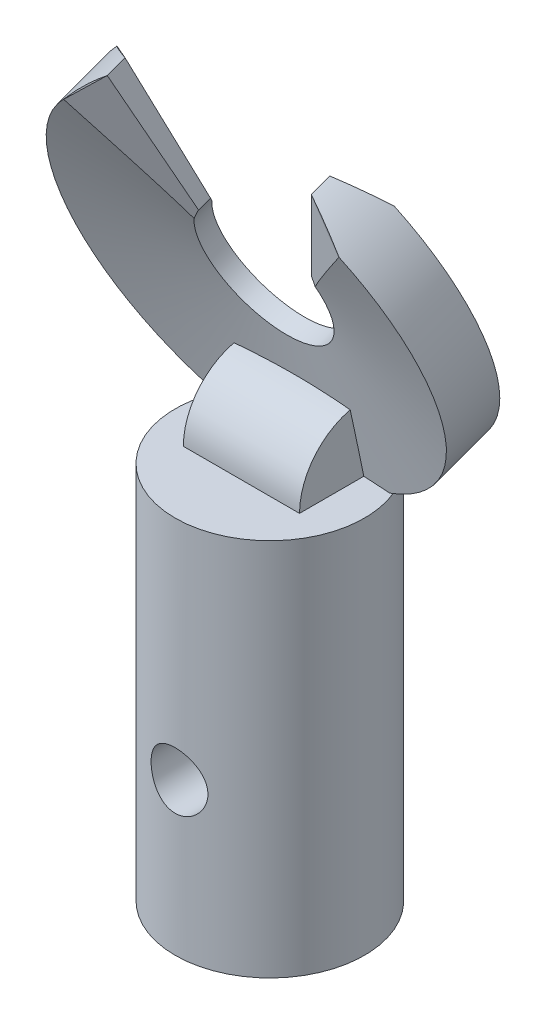
SolidWorks part; units mm, degrees
ref_plane "Front Plane" through (0, 0, 0) normal (0, 0, 1) x (1, 0, 0)
ref_plane "Top Plane" through (0, 0, 0) normal (0, 1, 0) x (1, 0, 0)
ref_plane "Right Plane" through (0, 0, 0) normal (1, 0, 0) x (0, 0, -1)
sketch "Sketch1" plane through (0, 0, 0) normal (0, 1, 0) x (1, 0, 0)
  line L1 (-15, 15) -> (15, 15)
  line L2 (-15, 15) -> (-15, -15)
  line L3 (-15, -15) -> (15, -15)
  line L4 (15, 15) -> (15, -15)
  line L5 (-15, 15) -> (15, -15) construction
  line L6 (-15, -15) -> (15, 15) construction
  point P0 (0, 0)
  dimension "D1" = 30
  dimension "D2" = 30
extrude "Boss-Extrude1" add sketch "Sketch1" along normal blind 3
sketch "Sketch2" plane through (0, 3, 0) normal (0, 1, 0) x (1, 0, 0)
  circle A0 centre (0, -2) radius 5
extrude "Boss-Extrude2" add sketch "Sketch2" along normal blind 55
sketch "Sketch3" plane through (0, 58, 0) normal (0, 1, 0) x (1, 0, 0)
  line L0 (-4.505, 3) -> (6.0136, 3)
  line L1 (15, 15) -> (-15, 15) construction
  circle A1 centre (0, -2) radius 5 construction
ref_plane "Plane1" through (0, 7.7489, -21.2899) normal (0, 0.342, -0.9397) x (1, 0, 0)
sketch "Sketch4" plane through (0, 0, 0) normal (1, 0, 0) x (0, 0, -1)
  line L0 (2.9957, 58.0118) -> (0.1766, 56.9858)
  line L1 (27.1793, -8.432) -> (15.4005, 23.9298) construction
  line L2 (0.1766, 56.9858) -> (-1.1068, 63.4358)
  line L4 (-1.1068, 63.4358) -> (-0.1671, 63.7778)
  line L6 (-0.1671, 63.7778) -> (2.9957, 58.0118)
  line L7 (1.5862, 57.4988) -> (-3.4595, 71.3617) construction
  line L8 (2.1162, 68.3335) -> (-6.6807, 65.1317) construction
  dimension "D1" = 3
  dimension "D2" = 1
  dimension "D3" = 0.5
  dimension "D4" = 6.5
  dimension "D5" = 10
revolve "Revolve1" add sketch "Sketch4" angle 360 about L8
sketch "Sketch5" plane through (0, 7.7489, -21.2899) normal (0, 0.342, -0.9397) x (1, 0, 0)
  line L0 (0, -64.2507) -> (0, -78.6334) construction
  line L1 (-3, -65.2915) -> (-6.5722, -75.1059)
  line L2 (3, -65.2915) -> (6.5722, -75.1059)
  line L3 (-3, -65.2915) -> (3, -65.2915)
  line L4 (-6.5722, -75.1059) -> (6.5722, -75.1059)
  circle A0 centre (0, -63.4887) radius 3.5 construction
  dimension "D1" = 20
  dimension "D2" = 3
extrude "Cut-Extrude2" cut sketch "Sketch5" against normal blind 55
ref_plane "Plane2" through (37.6382, 42.1503, 15.3415) normal (0.6428, 0.7198, 0.262) x (0, -0.342, 0.9397)
sketch "Sketch6" plane through (37.6382, 42.1503, 15.3415) normal (0.6428, 0.7198, 0.262) x (0, -0.342, 0.9397)
  line L0 (-22.6562, -42.0763) -> (-22.6562, -39.5763)
  line L1 (-22.6562, -39.5763) -> (-21.6562, -42.0763)
  line L2 (-22.6562, -42.0763) -> (-19.6562, -42.0763) construction
  line L3 (-21.6562, -42.0763) -> (-22.6562, -42.0763)
  line L4 (-21.1363, -42.0763) -> (-21.1363, -38.1037) construction
  line L5 (-19.6163, -42.0763) -> (-19.6163, -39.5763)
  line L6 (-20.6163, -42.0763) -> (-19.6163, -42.0763)
  line L7 (-19.6163, -39.5763) -> (-20.6163, -42.0763)
  dimension "D1" = 1
  dimension "D2" = 2.5
extrude "Cut-Extrude3" cut sketch "Sketch6" against normal blind 7 draft 9 and the other way blind 2 draft outward yes
ref_plane "Plane3" through (-37.6382, 42.1503, 15.3415) normal (0.6428, -0.7198, -0.262) x (0, 0.342, -0.9397)
sketch "Sketch8" plane through (-37.6382, 42.1503, 15.3415) normal (0.6428, -0.7198, -0.262) x (0, 0.342, -0.9397)
  line L0 (22.6562, 42.0763) -> (22.6562, 39.5763)
  line L1 (22.6562, 39.5763) -> (21.6562, 42.0763)
  line L2 (19.6562, 42.0763) -> (22.6562, 42.0763) construction
  line L3 (21.6562, 42.0763) -> (22.6562, 42.0763)
  line L4 (21.1562, 42.0763) -> (21.1562, 37.0421) construction
  line L5 (20.6562, 42.0763) -> (19.6562, 42.0763)
  line L6 (19.6562, 42.0763) -> (19.6562, 39.5763)
  line L7 (19.6562, 39.5763) -> (20.6562, 42.0763)
  dimension "D1" = 1
  dimension "D2" = 2.5
extrude "Cut-Extrude4" cut sketch "Sketch8" along normal blind 7 draft 9 and the other way blind 2 draft 9
sketch "Sketch10" plane through (0, 58, 0) normal (0, 1, 0) x (1, 0, 0)
  line L0 (-4.5826, 0) -> (4.5826, 0)
  arc A1 (-4.5826, 0) -> (4.5826, 0) centre (0, -2) ccw
  circle A2 centre (0, -2) radius 5 construction
  dimension "D2" = 10
revolve "Revolve2" [suppressed] add sketch "Sketch10" angle 90 about L0
sketch "Sketch11" plane through (0, 0, 0) normal (1, 0, 0) x (0, 0, -1)
  line L1 (-18.3794, -2.1859) -> (24.0775, -2.1859)
  line L2 (-18.3794, -2.1859) -> (-18.3794, 37.7012)
  line L3 (-18.3794, 37.7012) -> (24.0775, 37.7012)
  line L4 (24.0775, -2.1859) -> (24.0775, 37.7012)
extrude "Cut-Extrude5" cut sketch "Sketch11" against normal through all and the other way through all
sketch "Sketch12" plane through (0, 37.7012, 0) normal (0, -1, 0) x (1, 0, 0)
  line L1 (-15, 15) -> (15, 15)
  line L2 (-15, 15) -> (-15, -15)
  line L3 (-15, -15) -> (15, -15)
  line L4 (15, 15) -> (15, -15)
  line L5 (-15, 15) -> (15, -15) construction
  line L6 (-15, -15) -> (15, 15) construction
  point P0 (0, 0)
  dimension "D1" = 30
  dimension "D2" = 30
extrude "Boss-Extrude3" add sketch "Sketch12" along normal blind 3
sketch "Sketch13" plane through (0, 58, 0) normal (0, 1, 0) x (1, 0, 0)
  line L1 (-3.0674, 0) -> (3.0674, 0)
  line L3 (-3.0674, 0) -> (-3.0674, -3.5)
  line L4 (-3.0674, -3.5) -> (3.0674, -3.5)
  line L5 (3.0674, 0) -> (3.0674, -3.5)
  dimension "D1" = 3.5
revolve "Revolve3" add sketch "Sketch13" angle 90 about L1
sketch "Sketch14" plane through (0, 34.7012, 0) normal (0, -1, 0) x (1, 0, 0)
  line L1 (-18.3486, -16.2388) -> (15.9794, -16.2388)
  line L2 (-18.3486, -16.2388) -> (-18.3486, 17.8046)
  line L3 (-18.3486, 17.8046) -> (15.9794, 17.8046)
  line L4 (15.9794, -16.2388) -> (15.9794, 17.8046)
  line L5 (-18.3486, -16.2388) -> (15.9794, 17.8046) construction
  line L6 (-18.3486, 17.8046) -> (15.9794, -16.2388) construction
  point P2 (-1.1846, 0.7829)
extrude "Cut-Extrude6" cut sketch "Sketch14" against normal blind 3.3
sketch "Sketch17" plane through (0, 38.0012, 0) normal (0, -1, 0) x (1, 0, 0)
  line L0 (0, 7) -> (0, -3) construction
  line L1 (-5, 2) -> (5, 2) construction
  circle A0 centre (0, 2) radius 5 construction
  circle A1 centre (0, 2) radius 2
  dimension "D1" = 4
extrude "Cut-Extrude7" cut sketch "Sketch17" against normal blind 18
sketch "Sketch18" plane through (0, 0, 0) normal (0, 0, 1) x (1, 0, 0)
  line L0 (0, 37.1517) -> (0, 70.2808) construction
  line L1 (-5, 38.0012) -> (5, 38.0012) construction
  circle A0 centre (0, 46.0012) radius 1.5
  dimension "D1" = 3
  dimension "D2" = 8
extrude "Cut-Extrude8" cut sketch "Sketch18" against normal through all and the other way through all
